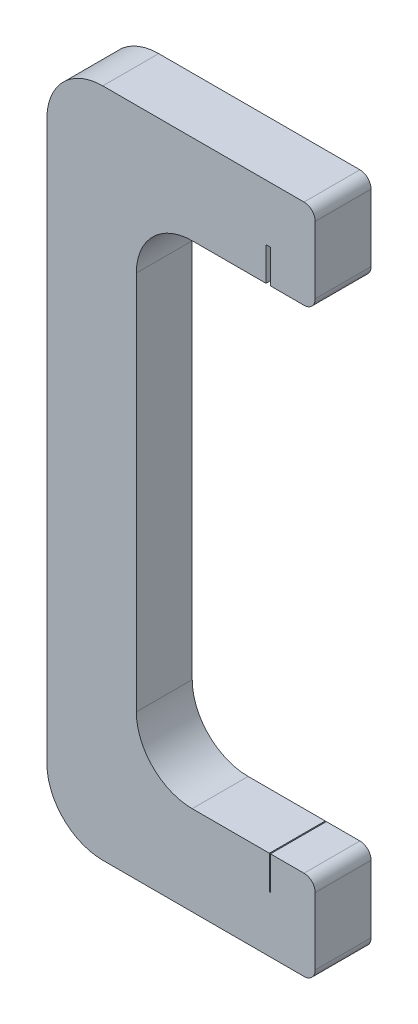
SolidWorks part; units mm, degrees
ref_plane "Front Plane" through (0, 0, 0) normal (0, 0, 1) x (1, 0, 0)
ref_plane "Top Plane" through (0, 0, 0) normal (0, 1, 0) x (1, 0, 0)
ref_plane "Right Plane" through (0, 0, 0) normal (1, 0, 0) x (0, 0, -1)
sketch "Sketch1" plane through (0, 0, 0) normal (0, 0, 1) x (1, 0, 0)
  line L0 (0, 55) -> (0, 5)
  line L1 (5, 0) -> (23, 0)
  line L2 (24, 1) -> (24, 7)
  line L3 (23, 8) -> (13, 8)
  line L4 (8, 13) -> (8, 47)
  line L5 (13, 52) -> (23, 52)
  line L6 (24, 53) -> (24, 59)
  line L7 (23, 60) -> (5, 60)
  arc A0 (5, 60) -> (0, 55) centre (5, 55) ccw
  arc A1 (13, 52) -> (8, 47) centre (13, 47) ccw
  arc A2 (13, 8) -> (8, 13) centre (13, 13) cw
  arc A3 (5, 0) -> (0, 5) centre (5, 5) cw
  arc A4 (24, 59) -> (23, 60) centre (23, 59) ccw
  arc A5 (24, 53) -> (23, 52) centre (23, 53) cw
  arc A6 (24, 1) -> (23, 0) centre (23, 1) cw
  arc A7 (24, 7) -> (23, 8) centre (23, 7) ccw
  point P11 (0, 60)
  point P18 (0, 0)
  point P21 (24, 60)
  point P24 (24, 52)
  point P27 (24, 0)
  point P30 (24, 8)
  dimension "D6" = 5
  dimension "D7" = 5
  dimension "D8" = 5
  dimension "D9" = 5
  dimension "D10" = 1
  dimension "D1" = 60
  dimension "D2" = 8
  dimension "D3" = 8
  dimension "D4" = 16
  dimension "D5" = 8
extrude "Boss-Extrude1" add sketch "Sketch1" along normal blind 5
sketch "Sketch3" plane through (0, 8, 0) normal (0, 1, 0) x (1, 0, 0)
  line L0 (0, -2.5) -> (19.95, -2.5) construction
  line L1 (0, -5) -> (0, 0) construction
  line L2 (23, 0) -> (13, 0) construction
  line L3 (19.9, -5) -> (20, -5)
  line L4 (19.9, -5) -> (19.9, 0)
  line L5 (19.9, 0) -> (20, 0)
  line L6 (20, -5) -> (20, 0)
  line L7 (19.9, -5) -> (20, 0) construction
  line L8 (19.9, 0) -> (20, -5) construction
  dimension "D1" = 19.95
  dimension "D2" = 0.1
extrude "Cut-Extrude1" cut sketch "Sketch3" against normal blind 3
sketch "Sketch4" plane through (0, 52, 0) normal (0, -1, 0) x (1, 0, 0)
  line L0 (0, 2.5) -> (19.8, 2.5) construction
  line L1 (0, 5) -> (0, 0) construction
  line L2 (13, 5) -> (23, 5) construction
  line L3 (19.6, 0) -> (20, 0)
  line L4 (19.6, 0) -> (19.6, 5)
  line L5 (19.6, 5) -> (20, 5)
  line L6 (20, 0) -> (20, 5)
  line L7 (19.6, 0) -> (20, 5) construction
  line L8 (19.6, 5) -> (20, 0) construction
  dimension "D1" = 19.8
  dimension "D2" = 0.4
extrude "Cut-Extrude2" cut sketch "Sketch4" against normal blind 3
equation "\"A.L\"= 0.07m"
equation "\"A.h\"= 0.007m"
equation "\"A.d\"= 0.005m"
equation "\"A.delta\"= 45.0001"
equation "\"A.w\"= 0m"
equation "\"A.v\"= 0.013m"
equation "\"A.s\"= 0.014m"
equation "\"A.t\"= 0.007m"
equation "\"B.L\"= 0.065m"
equation "\"B.h\"= 0.008m"
equation "\"B.s\"= 0.016m"
equation "\"B.t\"= 0.008m"
equation "\"C.h\"= 0.0065m"
equation "\"C.d\"= 0.005m"
equation "\"C.L\"= 0.05m"
equation "\"C.wmax\"= 0.003m"
equation "\"D.L\"= 0.06m"
equation "\"D.h\"= 0.008m"
equation "\"D.s\"= 0.012m"
equation "\"D.t\"= 0.008m"
equation "\"a_h\"= 0.0001m"
equation "\"a_d\"= 0.005m"
equation "\"a_L\"= 0.008m"
equation "\"b_h\"= 0.0004m"
equation "\"b_d\"= 0.005m"
equation "\"b_L\"= 0.007m"
equation "\"c_h\"= 0.0001m"
equation "\"c_d\"= 0.005m"
equation "\"c_L\"= 0.01m"
equation "\"d_h\"= 0.0001m"
equation "\"d_d\"= 0.005m"
equation "\"d_L\"= 0.01m"
equation "\"S.h\"= 0.015m"
equation "\"S.L\"= 0.09275m"
equation "\"D1@Sketch1\"=\"D.L\""
equation "\"D2@Sketch1\"=\"D.h\""
equation "\"D3@Sketch1\"=\"D.h\""
equation "\"D4@Sketch1\"=\"D.s\"+0.004"
equation "\"D5@Sketch1\"=\"D.h\""
equation "\"D1@Boss-Extrude1\"=\"A.d\""
equation "\"D1@Sketch3\"=\"D.h\"+\"D.s\"-\"a_h\"/2"
equation "\"D2@Sketch3\"=\"a_h\""
equation "\"D1@Sketch4\"=\"D.h\"+\"D.s\"-\"b_h\"/2"
equation "\"D2@Sketch4\"=\"b_h\""
